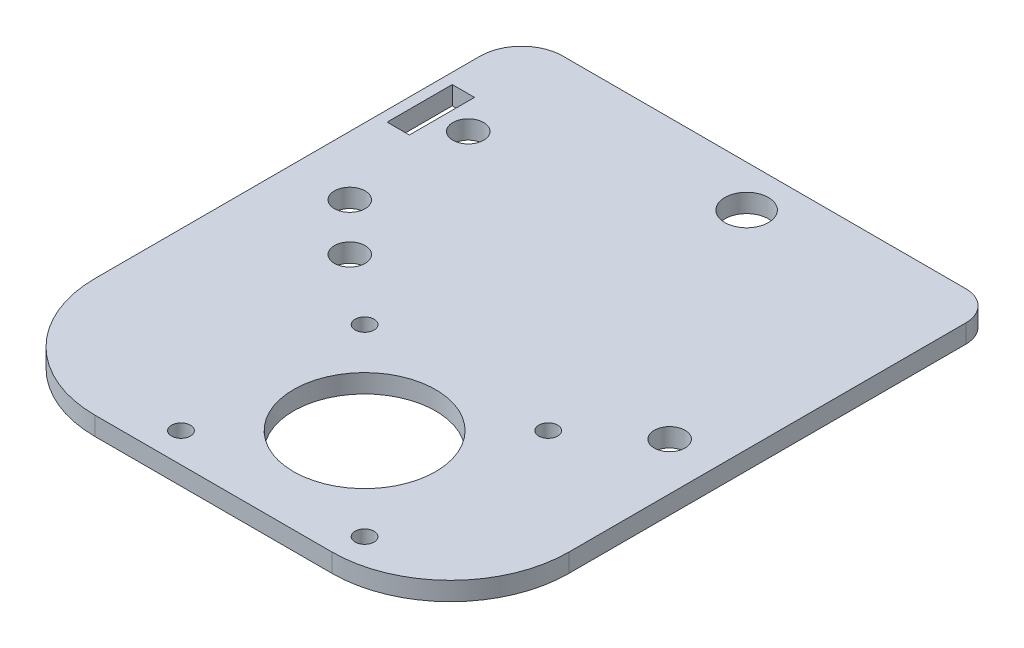
SolidWorks part; units mm, degrees
ref_plane "Front Plane" through (0, 0, 0) normal (0, 0, 1) x (1, 0, 0)
ref_plane "Top Plane" through (0, 0, 0) normal (0, 1, 0) x (1, 0, 0)
ref_plane "Right Plane" through (0, 0, 0) normal (1, 0, 0) x (0, 0, -1)
sketch "Sketch2" plane through (0, 0, 0) normal (0, 1, 0) x (1, 0, 0)
  line L0 (0, 0) -> (0, 92)
  line L1 (0, 92) -> (80, 92)
  line L2 (80, 92) -> (80, 0)
  line L3 (80, 0) -> (0, 0)
  line L5 (29.5, 36) -> (60.5, 36) construction
  line L6 (60.5, 36) -> (60.5, 5) construction
  line L7 (60.5, 5) -> (29.5, 5) construction
  line L8 (29.5, 5) -> (29.5, 36) construction
  line L9 (1.8, 78.5) -> (1.8, 67.5)
  line L10 (1.8, 67.5) -> (5.5607, 67.5)
  line L11 (5.5607, 67.5) -> (5.5607, 78.5)
  line L12 (7.1607, 76.9) -> (4.5, 79.5607) construction
  line L13 (5.5607, 78.5) -> (1.8, 78.5)
  circle A0 centre (29.5, 5) radius 1.6
  circle A1 centre (29.5, 36) radius 1.6
  circle A2 centre (60.5, 36) radius 1.6
  circle A3 centre (60.5, 5) radius 1.6
  circle A4 centre (18, 45) radius 2.6
  circle A5 centre (72, 45) radius 2.6
  circle A6 centre (45, 20.5) radius 12
  circle A7 centre (45, 85) radius 3.675
  circle A8 centre (10, 53) radius 2.6
  circle A9 centre (10, 73) radius 2.6
  dimension "D6" = 3.2
  dimension "D7" = 5.2
  dimension "D11" = 15.5
  dimension "D12" = 24
  dimension "D13" = 31
  dimension "D3" = 5
  dimension "D14" = 31
  dimension "D15" = 31
  dimension "D16" = 15.5
  dimension "D17" = 31
  dimension "D18" = 10
  dimension "D19" = 5.2
  dimension "D4" = 7.35
  dimension "D5" = 35
  dimension "D21" = 40
  dimension "D22" = 54
  dimension "D8" = 8
  dimension "D9" = 19.5
  dimension "D23" = 53
  dimension "D25" = 10
  dimension "D1" = 80
  dimension "D10" = 45
  dimension "D20" = 92
  dimension "D24" = 20
extrude "Boss-Extrude1" add sketch "Sketch2" along normal blind 3.125
fillet "Fillet1" radius 20 1 edges at (80, 1.5625, 0)
fillet "Fillet2" radius 20 1 edges at (0, 1.5625, 0)
fillet "Fillet4" radius 5 1 edges at (80, 1.5625, -92)
fillet "Fillet5" radius 7 1 edges at (0, 1.5625, -92)
